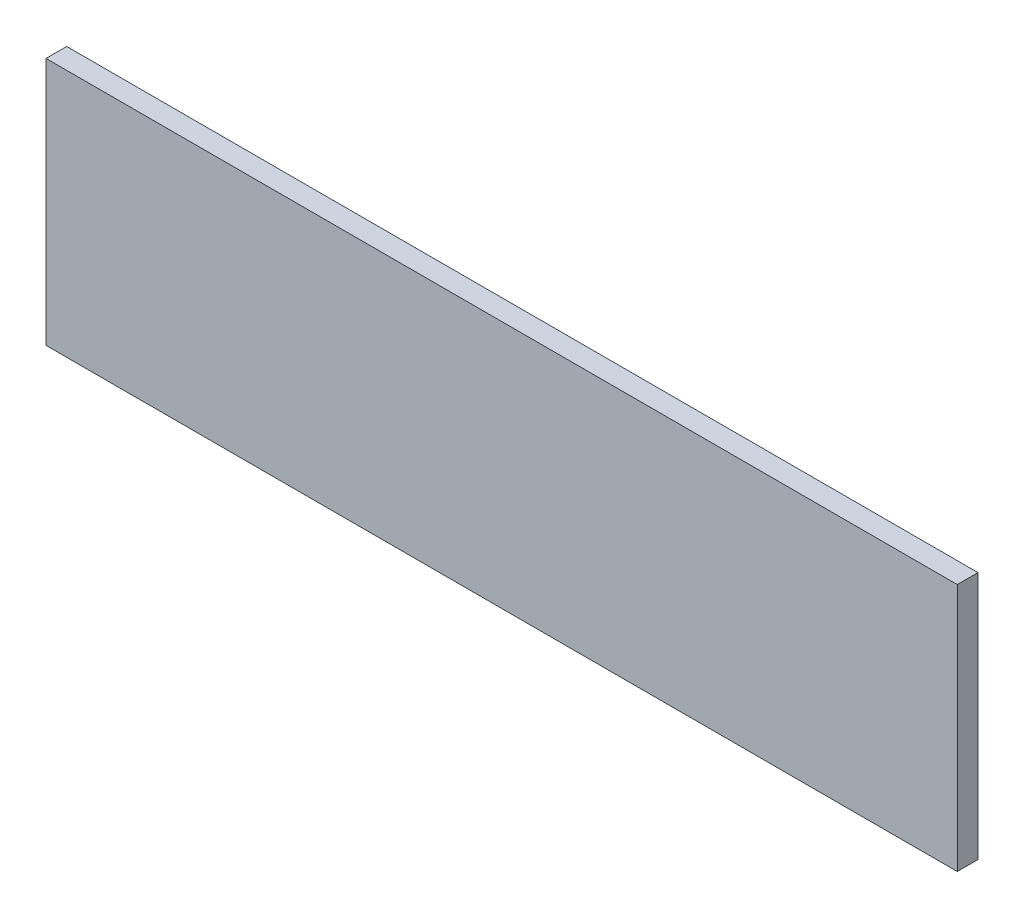
SolidWorks part; units mm, degrees
ref_plane "Front Plane" through (0, 0, 0) normal (0, 0, 1) x (1, 0, 0)
ref_plane "Top Plane" through (0, 0, 0) normal (0, 1, 0) x (1, 0, 0)
ref_plane "Right Plane" through (0, 0, 0) normal (1, 0, 0) x (0, 0, -1)
sketch "Sketch1" plane through (0, 0, 0) normal (0, 0, 1) x (1, 0, 0)
  line L1 (0, 0) -> (279.4, 0)
  line L2 (0, 0) -> (0, 76.2)
  line L3 (0, 76.2) -> (279.4, 76.2)
  line L4 (279.4, 0) -> (279.4, 76.2)
  dimension "D1" = 279.4
  dimension "D2" = 76.2
extrude "Boss-Extrude1" add sketch "Sketch1" along normal blind 6.35
